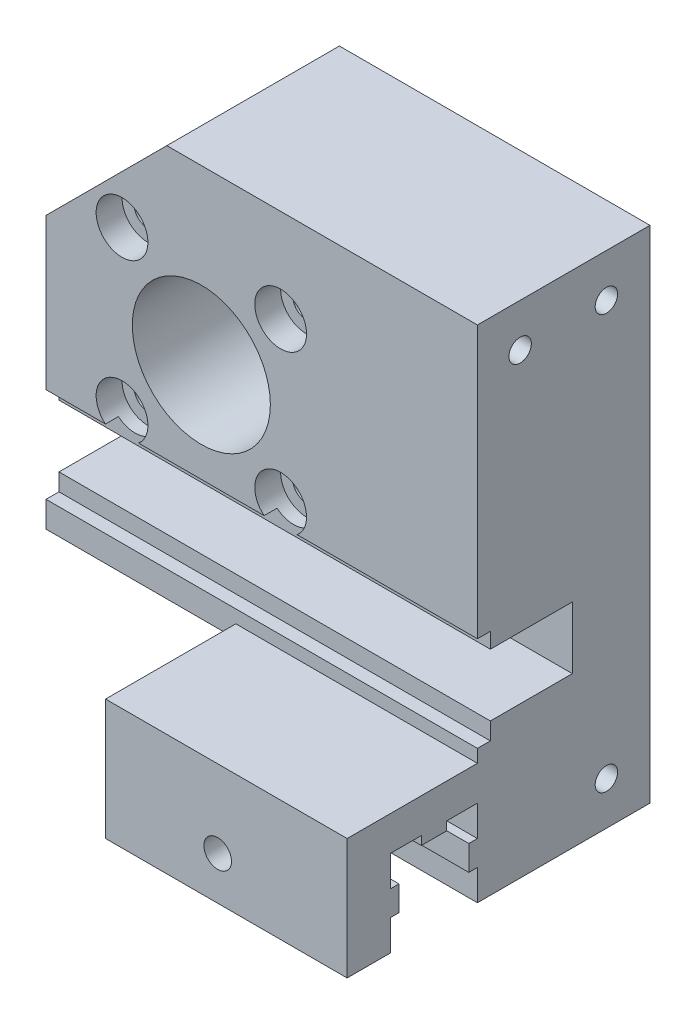
SolidWorks part; units mm, degrees
ref_plane "Front Plane" through (0, 0, 0) normal (0, 0, 1) x (1, 0, 0)
ref_plane "Top Plane" through (0, 0, 0) normal (0, 1, 0) x (1, 0, 0)
ref_plane "Right Plane" through (0, 0, 0) normal (1, 0, 0) x (0, 0, -1)
sketch "Esquisse1" plane through (0, 0, 0) normal (0, 0, 1) x (1, 0, 0)
  line L0 (25, 22.5) -> (25, -22.5)
  line L1 (-25, 22.5) -> (25, 22.5)
  line L2 (-25, 22.5) -> (-25, -22.5)
  line L3 (-25, -22.5) -> (25, -22.5)
  point P4 (-25, 0)
  point P6 (0, -22.5)
  dimension "D3" = 45
  dimension "D4" = 50
extrude "Main Extrusion" add sketch "Esquisse1" along normal blind 20
sketch "Esquisse5" plane through (0, 0, 20) normal (0, 0, 1) x (1, 0, 0)
  line L1 (-25, -22.5) -> (25, -22.5) construction
  line L3 (-25, 22.5) -> (-25, -22.5) construction
  circle A0 centre (-7, 2.5) radius 8
  dimension "D1" = 16
  dimension "D2" = 25
  dimension "D3" = 18
extrude "Gear Linear Holes" cut sketch "Esquisse5" against normal through all
sketch "Esquisse8" plane through (0, 0, 0) normal (1, 0, 0) x (0, 0, -1)
  line L0 (-20, -25.5) -> (-20, -29.05)
  line L1 (-20, -25.5) -> (-23.6, -25.5)
  line L2 (-23.6, -25.5) -> (-23.6, -26.5)
  line L3 (-23.6, -26.5) -> (-26.5, -26.5)
  line L4 (-26.5, -26.5) -> (-26.5, -25.5)
  line L5 (-35.1, -21.5) -> (0, -21.5)
  line L6 (-20, -35.5) -> (0, -35.5)
  line L7 (0, -35.5) -> (0, -21.5)
  line L8 (0, -22.5) -> (0, 22.5) construction
  line L9 (-26.5, -25.5) -> (-30.1, -25.5)
  line L10 (-20, -22.5) -> (0, -22.5) construction
  line L12 (0, 22.5) -> (0, -22.5) construction
  line L13 (-30.1, -25.5) -> (-30.1, -29.05)
  line L14 (-30.1, -35.5) -> (-35.1, -35.5)
  line L15 (-35.1, -35.5) -> (-35.1, -21.5)
  line L16 (-20, -29.05) -> (-21, -29.05)
  line L17 (-21, -29.05) -> (-21, -31.95)
  line L18 (-21, -31.95) -> (-20, -31.95)
  line L19 (-20, -31.95) -> (-20, -35.5)
  line L21 (-30.1, -29.05) -> (-29.1, -29.05)
  line L22 (-29.1, -29.05) -> (-29.1, -31.95)
  line L23 (-29.1, -31.95) -> (-30.1, -31.95)
  line L24 (-30.1, -31.95) -> (-30.1, -35.5)
  line L25 (-20, 22.5) -> (-20, -22.5) construction
  dimension "D1" = 2.9
  dimension "D2" = 10.1
  dimension "D3" = 1
  dimension "D4" = 3
  dimension "D5" = 10
  dimension "D6" = 5
  dimension "D7" = 4
extrude "Fixing Extrusion" add sketch "Esquisse8" along normal mid plane 50
sketch "Esquisse12" plane through (0, 0, 0) normal (0, 0, 1) x (1, 0, 0)
  circle A0 centre (-7, 2.5) radius 16
  dimension "D1" = 32
sketch "Esquisse13" plane through (0, 0, 20) normal (0, 0, 1) x (1, 0, 0)
  line L0 (-25, 22.5) -> (-25, -21.5) construction
  line L1 (-25, -18) -> (25, -18)
  line L2 (-25, -18) -> (-25, -10.8)
  line L3 (-25, -10.8) -> (25, -10.8)
  line L4 (25, -18) -> (25, -10.8)
  line L5 (25, -21.5) -> (25, 22.5) construction
  line L7 (-25, -21.5) -> (25, -21.5) construction
  dimension "D1" = 3.5
  dimension "D2" = 7.2
extrude "RollingBallHorizontalHole" cut sketch "Esquisse13" against normal blind 11
sketch "Esquisse14" plane through (-25, 0, 0) normal (-1, 0, 0) x (0, 0, 1)
  line L0 (0, -23) -> (20, -23)
  line L1 (0, -35.5) -> (35.1, -35.5)
  line L2 (0, -35.5) -> (0, -23)
  line L3 (20, -23) -> (20, -18)
  line L4 (35.1, -35.5) -> (35.1, -18)
  line L5 (20, -18) -> (35.1, -18)
  line L6 (20, -18) -> (20, -21.5) construction
  dimension "D1" = 12.5
extrude "FrontHole" cut sketch "Esquisse14" against normal blind 22
sketch "Esquisse15" plane through (0, 0, 35.1) normal (0, 0, 1) x (1, 0, 0)
  line L1 (25, -21.5) -> (25, -35.5) construction
  line L4 (-3, -31.95) -> (-3, -29.05) construction
  circle A1 centre (10, -30.5) radius 1.6
  point P5 (-3, -30.5)
  dimension "D1" = 3.2
  dimension "D2" = 15
extrude "BottomFixingHole" cut sketch "Esquisse15" against normal through all
extrude "ReductorMainHole" cut sketch "Esquisse12" along normal blind 5
sketch "Esquisse16" plane through (0, 0, 5) normal (0, 0, -1) x (-1, 0, 0)
  line L0 (2.6411, 11.5) -> (11.3589, 11.5)
  line L1 (2.6411, -6.5) -> (11.3589, -6.5)
  arc A0 (2.6411, 11.5) -> (2.6411, -6.5) centre (7, 2.5) ccw
  arc A2 (11.3589, 11.5) -> (11.3589, -6.5) centre (7, 2.5) cw
  circle A3 centre (7, 2.5) radius 16 construction
  dimension "D1" = 10
  dimension "D2" = 18
extrude "ReductorFrontFixingHole" cut sketch "Esquisse16" against normal blind 3
sketch "Esquisse17" plane through (0, 0, 5) normal (0, 0, -1) x (-1, 0, 0)
  line L0 (7, 2.5) -> (-2.1924, 11.6924) construction
  line L1 (19.305, 0) -> (-19.305, 0) construction
  line L2 (-2.1924, -6.6924) -> (16.1924, 11.6924) construction
  line L3 (7, 2.5) -> (16.1924, -6.6924) construction
  circle A0 centre (-2.1924, 11.6924) radius 1.6
  circle A1 centre (16.1924, 11.6924) radius 1.6
  circle A2 centre (-2.1924, -6.6924) radius 1.6
  circle A3 centre (16.1924, -6.6924) radius 1.6
  dimension "D1" = 3.2
  dimension "D2" = 45
  dimension "D3" = 13
  dimension "D4" = 13
  dimension "D5" = 13
extrude "MotorFixingHole" cut sketch "Esquisse17" against normal through all
sketch "Esquisse19" plane through (0, 0, 20) normal (0, 0, 1) x (1, 0, 0)
  circle A0 centre (-16.1924, 11.6924) radius 3
  circle A1 centre (2.1924, 11.6924) radius 3
  circle A2 centre (-16.1924, -6.6924) radius 3
  circle A3 centre (2.1924, -6.6924) radius 3
  dimension "D1" = 6
extrude "Enlèv. mat.-Extru.5" cut sketch "Esquisse19" against normal blind 3
sketch "Sketch2" plane through (25, 0, 0) normal (1, 0, 0) x (0, 0, -1)
  line L1 (-20, -20) -> (-18.5, -20)
  line L2 (-20, -20) -> (-20, -9)
  line L3 (-20, -9) -> (-18.5, -9)
  line L4 (-18.5, -20) -> (-18.5, -9)
  line L6 (-9, -18) -> (-20, -18) construction
  line L7 (-20, -10.8) -> (-20, 22.5) construction
  dimension "D1" = 11
  dimension "D2" = 1.5
  dimension "D3" = 2
extrude "CutForMakerBeamProfile" cut sketch "Sketch2" against normal through all
ref_plane "Plane1" through (0, 0, -5) normal (0, 0, 1) x (1, 0, 0)
sketch "Sketch3" plane through (0, 0, 20) normal (0, 0, 1) x (1, 0, 0)
  line L0 (-11, 22.5) -> (-25, 8.5)
  line L1 (25, 22.5) -> (-25, 22.5) construction
  line L2 (-25, 22.5) -> (-25, -9) construction
  line L3 (-25, 8.5) -> (-25, 22.5)
  line L4 (-25, 22.5) -> (-11, 22.5)
  dimension "D1" = 14
extrude "CutForDistributorGrabber" cut sketch "Sketch3" against normal through all
sketch "Sketch4" plane through (25, 0, 0) normal (1, 0, 0) x (0, 0, -1)
  line L0 (-30.1, -35.5) -> (-20, -25.5) construction
  line L1 (-30.1, -25.5) -> (-20, -35.5) construction
  line L2 (0, 22.5) -> (-20, 22.5) construction
  circle A0 centre (-5.05, -30.5) radius 1.3
  circle A1 centre (-25.05, -30.5) radius 1.3
  circle A2 centre (-5.05, 17.5) radius 1.3
  circle A3 centre (-15.05, 17.5) radius 1.3
  point P13 (-25.05, -30.5)
  dimension "D1" = 2.6
  dimension "D2" = 20
  dimension "D3" = 10
  dimension "D4" = 5
extrude "HoleToBlockBehind" cut sketch "Sketch4" against normal blind 12
